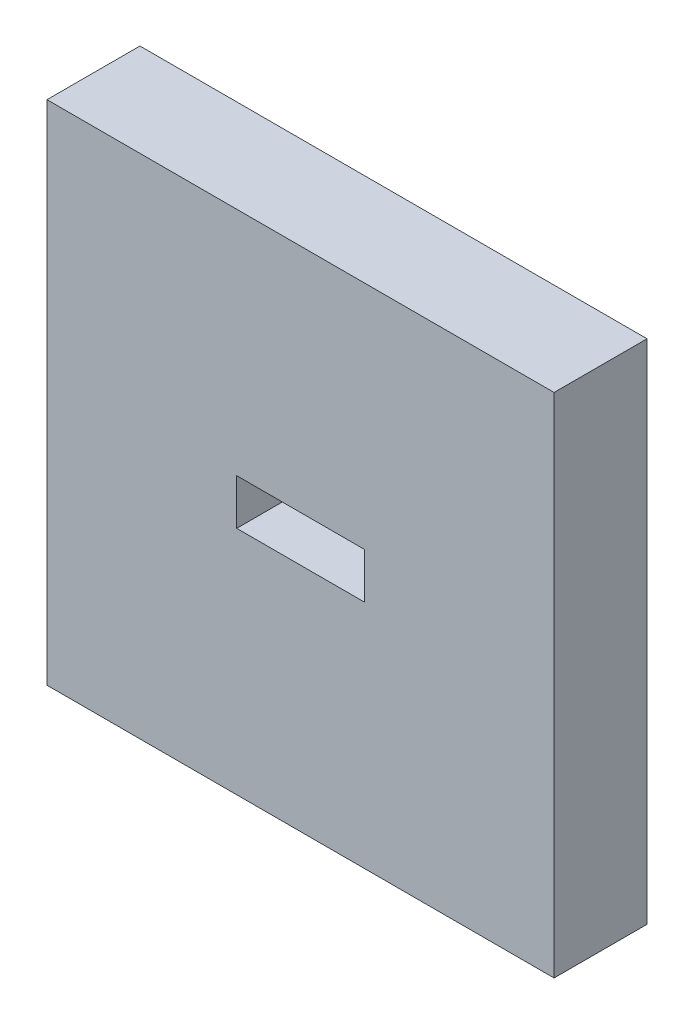
SolidWorks part; units mm, degrees
ref_plane "Спереди" through (0, 0, 0) normal (0, 0, 1) x (1, 0, 0)
ref_plane "Сверху" through (0, 0, 0) normal (0, 1, 0) x (1, 0, 0)
ref_plane "Справа" through (0, 0, 0) normal (1, 0, 0) x (0, 0, -1)
sketch "Эскиз1" plane through (0, 0, 0) normal (0, 0, 1) x (1, 0, 0)
  line L0 (75.5, 54) -> (75.5, 327) construction
  line L1 (0, 0) -> (151, 0)
  line L2 (0, 0) -> (0, 54)
  line L3 (0, 54) -> (151, 54)
  line L4 (151, 0) -> (151, 54)
  line L5 (-224.5, 327) -> (375.5, 327)
  line L6 (-224.5, 327) -> (-224.5, -273)
  line L7 (-224.5, -273) -> (375.5, -273)
  line L8 (375.5, 327) -> (375.5, -273)
  line L10 (-224.5, 27) -> (0, 27) construction
  dimension "D1" = 54
  dimension "D2" = 151
  dimension "D3" = 600
  dimension "D4" = 600
extrude "Бобышка-Вытянуть1" add sketch "Эскиз1" along normal blind 110
